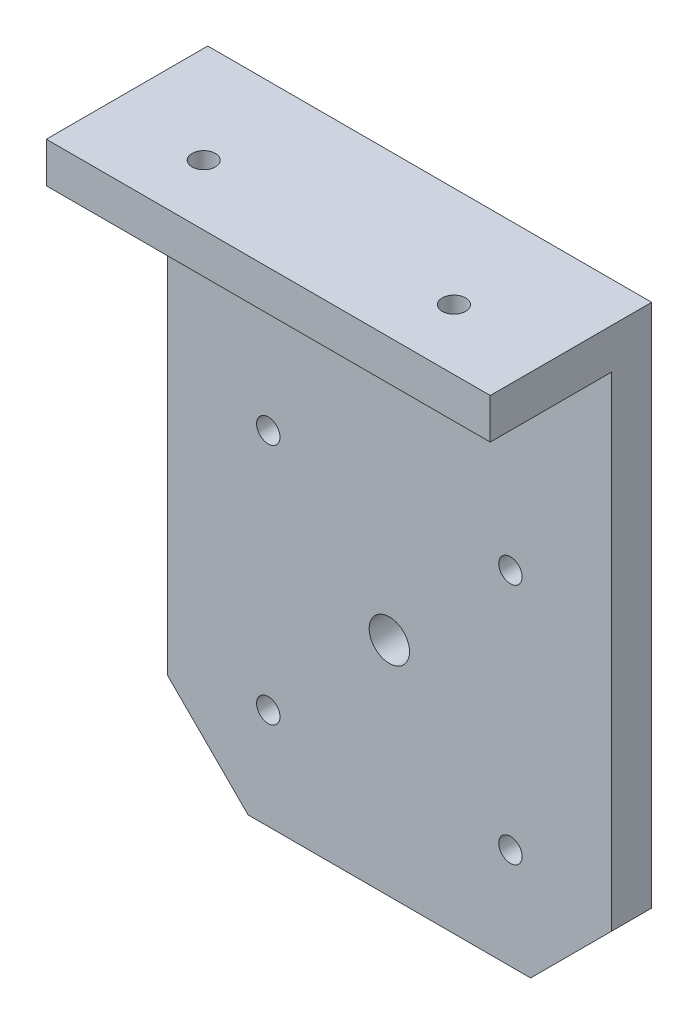
SolidWorks part; units mm, degrees
ref_plane "Ön Düzlem" through (0, 0, 0) normal (0, 0, 1) x (1, 0, 0)
ref_plane "Üst Düzlem" through (0, 0, 0) normal (0, 1, 0) x (1, 0, 0)
ref_plane "Sağ Düzlem" through (0, 0, 0) normal (1, 0, 0) x (0, 0, -1)
sketch "Sketch1" plane through (0, 0, 0) normal (0, 0, 1) x (1, 0, 0)
  line L0 (-17.5, -37.5) -> (-27.5, -27.5)
  line L1 (-27.5, 37.5) -> (27.5, 37.5)
  line L2 (-27.5, 37.5) -> (-27.5, -27.5)
  line L3 (-17.5, -37.5) -> (17.5, -37.5)
  line L4 (27.5, 37.5) -> (27.5, -27.5)
  line L5 (-27.5, 37.5) -> (23.2692, -31.7308) construction
  line L6 (-27.5, -37.5) -> (27.5, 37.5) construction
  line L7 (17.5, -37.5) -> (27.5, -27.5)
  point P0 (0, 0)
  dimension "D1" = 55
  dimension "D2" = 75
  dimension "D3" = 10
  dimension "D4" = 10
extrude "Boss-Extrude1" add sketch "Sketch1" along normal blind 5
sketch "Sketch2" plane through (0, 0, 5) normal (0, 0, 1) x (1, 0, 0)
  line L0 (-17.5, -37.5) -> (17.5, -37.5) construction
  line L1 (27.5, -27.5) -> (27.5, 37.5) construction
  circle A0 centre (0, -10) radius 2.5
  dimension "D1" = 27.5
  dimension "D2" = 27.5
extrude "Cut-Extrude1" cut sketch "Sketch2" against normal up to next
sketch "Sketch3" plane through (0, 0, 5) normal (0, 0, 1) x (1, 0, 0)
  line L0 (27.5, -27.5) -> (27.5, 37.5) construction
  line L1 (-27.5, 37.5) -> (27.5, 37.5)
  line L2 (-27.5, 37.5) -> (-27.5, 32.5)
  line L3 (-27.5, 32.5) -> (27.5, 32.5)
  line L4 (27.5, 37.5) -> (27.5, 32.5)
  dimension "D1" = 5
extrude "Boss-Extrude2" add sketch "Sketch3" along normal blind 15
hole_wizard "CSK for M2.5 Flat Head Machine Screw1" positions "Sketch5" profile "Sketch4" countersink size "M2.5" standard "ANSI Metric" end condition through all
sketch "Sketch5" plane through (0, 32.5, 0) normal (0, -1, 0) x (-1, 0, 0)
  line L0 (-27.5, -20) -> (-27.5, -5) construction
  line L2 (27.5, -20) -> (-27.5, -20) construction
  line L3 (27.5, -5) -> (-27.5, -5) construction
  line L4 (27.5, -20) -> (27.5, -5) construction
  point P0 (-15.5, -12.5)
  point P2 (15.5, -12.5)
  point P11 (-20.8281, -20)
  point P18 (-57.9755, -48.3958)
  point P25 (-43.0249, -55.2141)
  point P32 (-28.2906, -42.9951)
  dimension "D1" = 12
  dimension "D2" = 7.5
  dimension "D3" = 7.5
  dimension "D4" = 12
sketch "Sketch4" plane through (15.5, 32.5, 12.5) normal (1, 0, 0) x (0, 0, -1)
  line L0 (0, 0) -> (0, 5)
  line L1 (0, 5) -> (1.45, 5)
  line L2 (1.45, 5) -> (1.45, 1.3)
  line L3 (1.45, 1.3) -> (2.75, 0)
  line L5 (2.75, 0) -> (0, 0)
  line L6 (-1.45, 1.3) -> (-2.75, 0) construction
  line L11 (0, -6.35) -> (0, 107.95) construction
  dimension "Thru Hole Dia." = 2.9
  dimension "Thru Hole Depth" = 5
  dimension "Near C'Sink Dia." = 5.5
  dimension "Near C'Sink Angle" = 90
hole_wizard "CSK for M2.5 Flat Head Machine Screw2" positions "Sketch7" profile "Sketch6" countersink size "M2.5" standard "ANSI Metric" end condition up to next
sketch "Sketch7" plane through (0, 0, 0) normal (0, 0, -1) x (-1, 0, 0)
  point P0 (-15, 5)
  point P3 (15, 5)
  point P6 (-15, -25)
  point P9 (15, -25)
sketch "Sketch6" plane through (15, 5, 0) normal (1, 0, 0) x (0, 1, 0)
  line L0 (0, 0) -> (0, 5)
  line L1 (0, 5) -> (1.45, 5)
  line L2 (1.45, 5) -> (1.45, 1.3)
  line L3 (1.45, 1.3) -> (2.75, 0)
  line L5 (2.75, 0) -> (0, 0)
  line L6 (-1.45, 1.3) -> (-2.75, 0) construction
  line L11 (0, -6.35) -> (0, 107.95) construction
  dimension "Thru Hole Dia." = 2.9
  dimension "Thru Hole Depth" = 5
  dimension "Near C'Sink Dia." = 5.5
  dimension "Near C'Sink Angle" = 90
